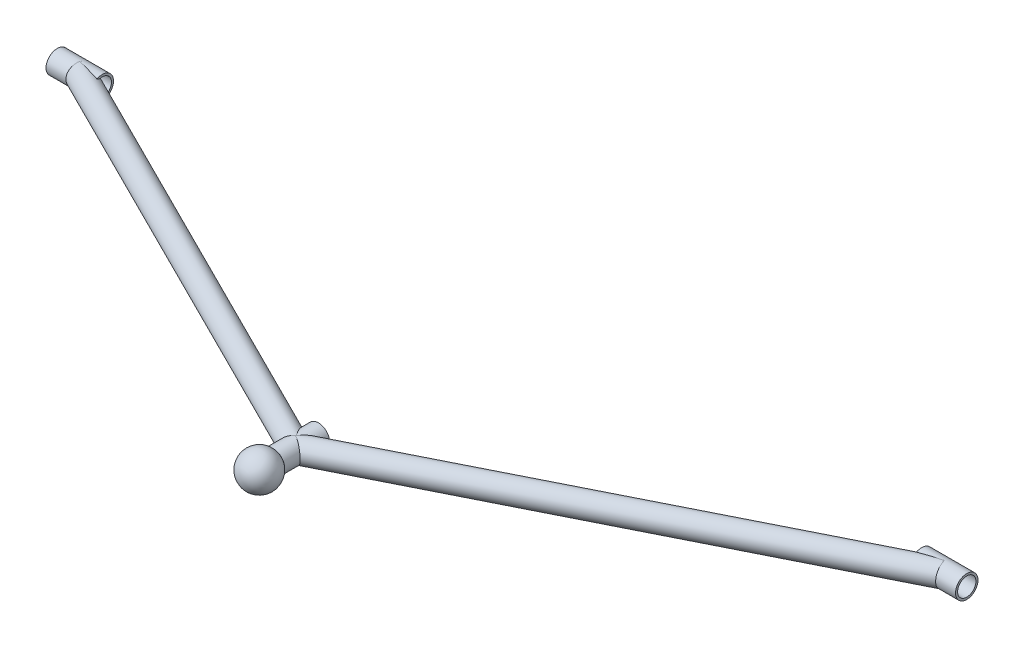
SolidWorks part; units mm, degrees
ref_plane "Front Plane" through (0, 0, 0) normal (0, 0, 1) x (1, 0, 0)
ref_plane "Top Plane" through (0, 0, 0) normal (0, 1, 0) x (1, 0, 0)
ref_plane "Right Plane" through (0, 0, 0) normal (1, 0, 0) x (0, 0, -1)
sketch "Sketch1" plane through (0, 0, 0) normal (0, 1, 0) x (1, 0, 0)
  line L0 (-304.8, 0) -> (304.8, 0) construction
  line L1 (-288.925, 0) -> (-320.675, 0)
  line L2 (0, 0) -> (0, -152.4) construction
  line L3 (0, -136.525) -> (0, -168.275)
  line L4 (-304.8, 0) -> (0, -152.4)
  line L5 (304.8, 0) -> (0, -152.4)
  line L6 (288.925, 0) -> (320.675, 0)
  point P4 (0, 0)
  point P7 (-304.8, 0)
  point P9 (304.8, 0)
  point P12 (0, -152.4)
  dimension "D1" = 609.6
  dimension "D2" = 31.75
  dimension "D3" = 152.4
  dimension "D4" = 31.75
other "Al round tubing AL RND TUBE 0.625 OD X 0.058 WALL(1)"
ref_plane "Plane1" through (-304.8, 0, 0) normal (0.8944, 0, 0.4472) x (0.4472, 0, -0.8944)
sketch "Sketch11" plane through (-304.8, 0, 0) normal (0.8944, 0, 0.4472) x (0.4472, 0, -0.8944)
  circle A0 centre (0, 0) radius 6.4643
  circle A1 centre (0, 0) radius 7.9375
  point P3 (0, 0)
  dimension "In_dia" = 12.9286
  dimension "Out_dia" = 15.875
other "Al round tubing AL RND TUBE 0.625 OD X 0.058 WALL(2)"
ref_plane "Plane2" through (0, 0, 136.525) normal (0, 0, 1) x (1, 0, 0)
sketch "Sketch12" plane through (0, 0, 136.525) normal (0, 0, 1) x (1, 0, 0)
  circle A0 centre (0, 0) radius 6.4643
  circle A1 centre (0, 0) radius 7.9375
  point P3 (0, 0)
  dimension "In_dia" = 12.9286
  dimension "Out_dia" = 15.875
sketch "Sketch13" plane through (0, 0, 0) normal (1, 0, 0) x (0, 0, -1)
  line L0 (-165.4889, 0) -> (-190.8889, 0)
  arc A0 (-165.4889, 0) -> (-190.8889, 0) centre (-178.1889, 0) ccw
  dimension "D1" = 25.4
revolve "Revolve1" add sketch "Sketch13" angle 360 about L0
